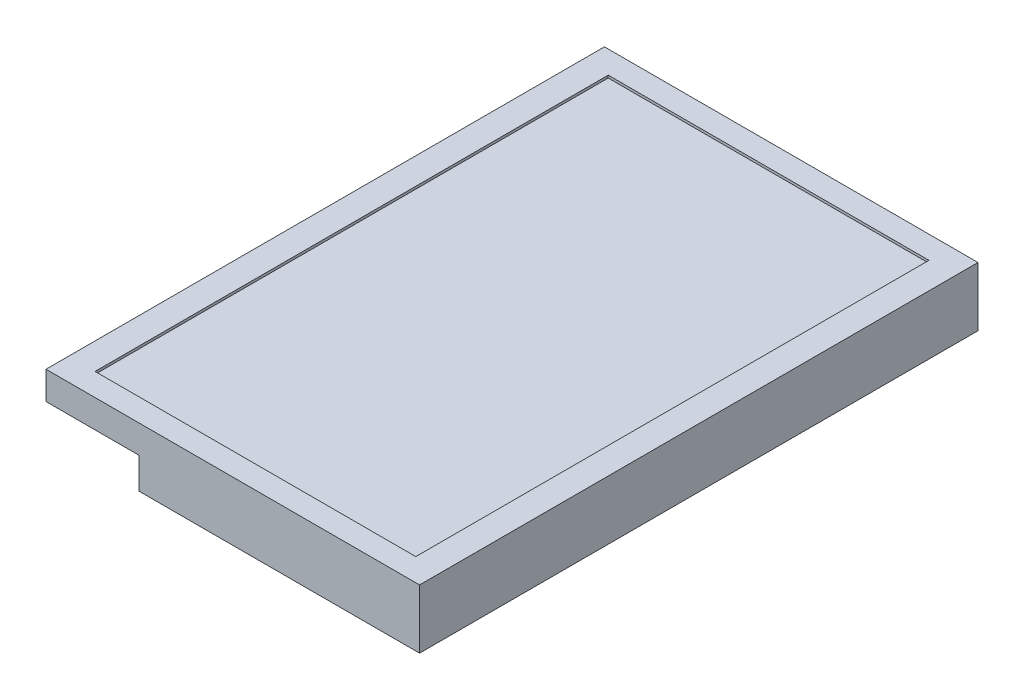
SolidWorks part; units mm, degrees
ref_plane "前基準面" through (0, 0, 0) normal (0, 0, 1) x (1, 0, 0)
ref_plane "上基準面" through (0, 0, 0) normal (0, 1, 0) x (1, 0, 0)
ref_plane "右基準面" through (0, 0, 0) normal (1, 0, 0) x (0, 0, -1)
sketch "草圖1" plane through (0, 0, 0) normal (0, 1, 0) x (1, 0, 0)
  line L1 (-148.5, -222) -> (148.5, -222)
  line L2 (-148.5, -222) -> (-148.5, 222)
  line L3 (-148.5, 222) -> (148.5, 222)
  line L4 (148.5, -222) -> (148.5, 222)
  line L5 (-148.5, -222) -> (148.5, 222) construction
  line L6 (-148.5, 222) -> (148.5, -222) construction
  point P0 (0, 0)
  dimension "D1" = 297
  dimension "D2" = 444
extrude "填料-伸長1" add sketch "草圖1" along normal blind 47
sketch "草圖2" plane through (0, 47, 0) normal (0, 1, 0) x (1, 0, 0)
  line L1 (-127.5, -204) -> (127.5, -204)
  line L2 (-127.5, -204) -> (-127.5, 204)
  line L3 (-127.5, 204) -> (127.5, 204)
  line L4 (127.5, -204) -> (127.5, 204)
  line L5 (-127.5, -204) -> (127.5, 204) construction
  line L6 (-127.5, 204) -> (127.5, -204) construction
  point P0 (0, 0)
  dimension "D1" = 255
  dimension "D2" = 408
extrude "除料-伸長1" cut sketch "草圖2" against normal blind 2
sketch "草圖3" plane through (0, 0, 0) normal (0, -1, 0) x (1, 0, 0)
  line L0 (148.5, -222) -> (-148.5, -222) construction
  line L1 (-148.5, 222) -> (-74.5, 222)
  line L2 (-148.5, 222) -> (-148.5, -222)
  line L3 (-148.5, -222) -> (-74.5, -222)
  line L4 (-74.5, 222) -> (-74.5, -222)
  dimension "D1" = 74
extrude "除料-伸長2" cut sketch "草圖3" against normal blind 24.7368
